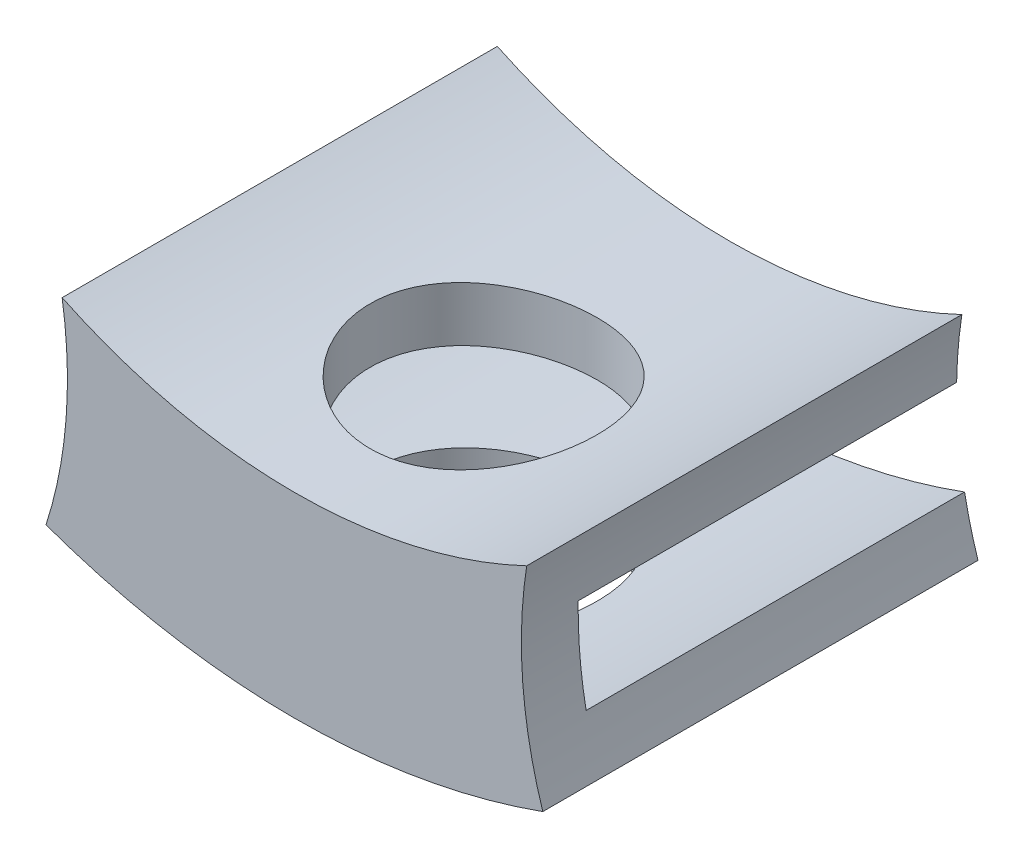
SolidWorks part; units mm, degrees
ref_plane "Front Plane" through (0, 0, 0) normal (0, 0, 1) x (1, 0, 0)
ref_plane "Top Plane" through (0, 0, 0) normal (0, 1, 0) x (1, 0, 0)
ref_plane "Right Plane" through (0, 0, 0) normal (1, 0, 0) x (0, 0, -1)
sketch "Sketch1" plane through (0, 0, 0) normal (0, 0, 1) x (1, 0, 0)
  arc A6 (12.2755, 39.1101) -> (13.1277, 28.286) centre (35.4954, 35.4928) ccw
  circle A7 centre (-35.4954, 35.4928) radius 23.5 construction
  arc A8 (-12.2753, 39.1089) -> (12.2755, 39.1101) centre (-0.0012, 64.8538) ccw
  circle A9 centre (35.4954, 35.4928) radius 23.5 construction
  arc A10 (-13.128, 28.2852) -> (13.1277, 28.286) centre (-0.0012, 64.8538) ccw
  arc A11 (-12.2753, 39.1089) -> (-13.128, 28.2852) centre (-35.4954, 35.4928) cw
extrude "Boss-Extrude1" add sketch "Sketch1" along normal blind 3
sketch "Sketch2" plane through (0, 0, 0) normal (0, 0, -1) x (-1, 0, 0)
  arc A0 (13.128, 28.2852) -> (12.4174, 31.0592) centre (35.4954, 35.4928) cw
  arc A1 (-0.0002, 33.4827) -> (11.9984, 35.8674) centre (0.0012, 64.8538) ccw
  arc A2 (12.2753, 39.1089) -> (13.128, 28.2852) centre (35.4954, 35.4928) ccw construction
  arc A3 (11.9984, 35.8674) -> (-11.9984, 35.8684) centre (0.0012, 64.8538) cw
  arc A4 (-13.1277, 28.286) -> (-12.2755, 39.1101) centre (-35.4954, 35.4928) ccw construction
  arc A5 (12.2753, 39.1089) -> (-12.2755, 39.1101) centre (0.0012, 64.8538) cw
  arc A6 (-17.0982, 20.871) -> (-34.8421, 12.0019) centre (-35.4954, 35.4928) ccw construction
  arc A7 (-11.9984, 35.8684) -> (-12.2755, 39.1101) centre (-35.4954, 35.4928) ccw
  arc A8 (11.9984, 35.8674) -> (12.2753, 39.1089) centre (35.4954, 35.4928) cw
  arc A11 (-13.1277, 28.286) -> (13.128, 28.2852) centre (0.0012, 64.8538) ccw
  arc A12 (12.4174, 31.0592) -> (-12.4172, 31.0601) centre (0.0012, 64.8538) cw
  arc A13 (-13.1277, 28.286) -> (-12.4172, 31.0601) centre (-35.4954, 35.4928) ccw
  arc M9 (13.128, 28.2852) -> (12.2753, 39.1089) centre (35.4954, 35.4928) cw
  arc M10 (12.2753, 39.1089) -> (-12.2755, 39.1101) centre (0.0012, 64.8538) cw
  arc M11 (-12.2755, 39.1101) -> (-13.1277, 28.286) centre (-35.4954, 35.4928) cw
  arc M12 (-13.1277, 28.286) -> (13.128, 28.2852) centre (0.0012, 64.8538) ccw
extrude "Boss-Extrude2" add sketch "Sketch2" along normal blind 20 contours A3 A1 M9 M10 M11 | A12 M9 M11 M12
sketch "Sketch3" plane through (0, 0, 0) normal (0, 1, 0) x (1, 0, 0)
  circle A0 centre (0.0001, 7) radius 6
extrude "Cut-Extrude1" cut sketch "Sketch3" along normal blind 58 contours A0
